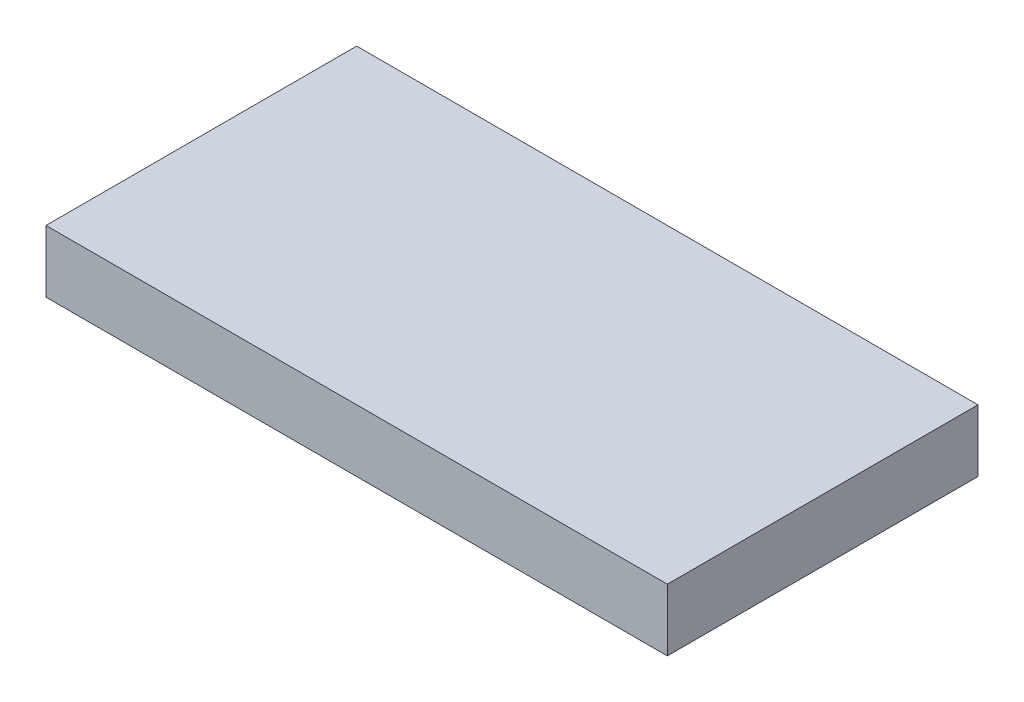
SolidWorks part; units mm, degrees
ref_plane "Front Plane" through (0, 0, 0) normal (0, 0, 1) x (1, 0, 0)
ref_plane "Top Plane" through (0, 0, 0) normal (0, 1, 0) x (1, 0, 0)
ref_plane "Right Plane" through (0, 0, 0) normal (1, 0, 0) x (0, 0, -1)
sketch "Sketch1" plane through (0, 0, 0) normal (0, 1, 0) x (1, 0, 0)
  line L1 (-6.8862, 48.8772) -> (93.1138, 48.8772)
  line L2 (-6.8862, 48.8772) -> (-6.8862, -1.1228)
  line L3 (-6.8862, -1.1228) -> (93.1138, -1.1228)
  line L4 (93.1138, 48.8772) -> (93.1138, -1.1228)
  dimension "D1" = 100
  dimension "D2" = 50
extrude "Boss-Extrude1" add sketch "Sketch1" along normal blind 10
